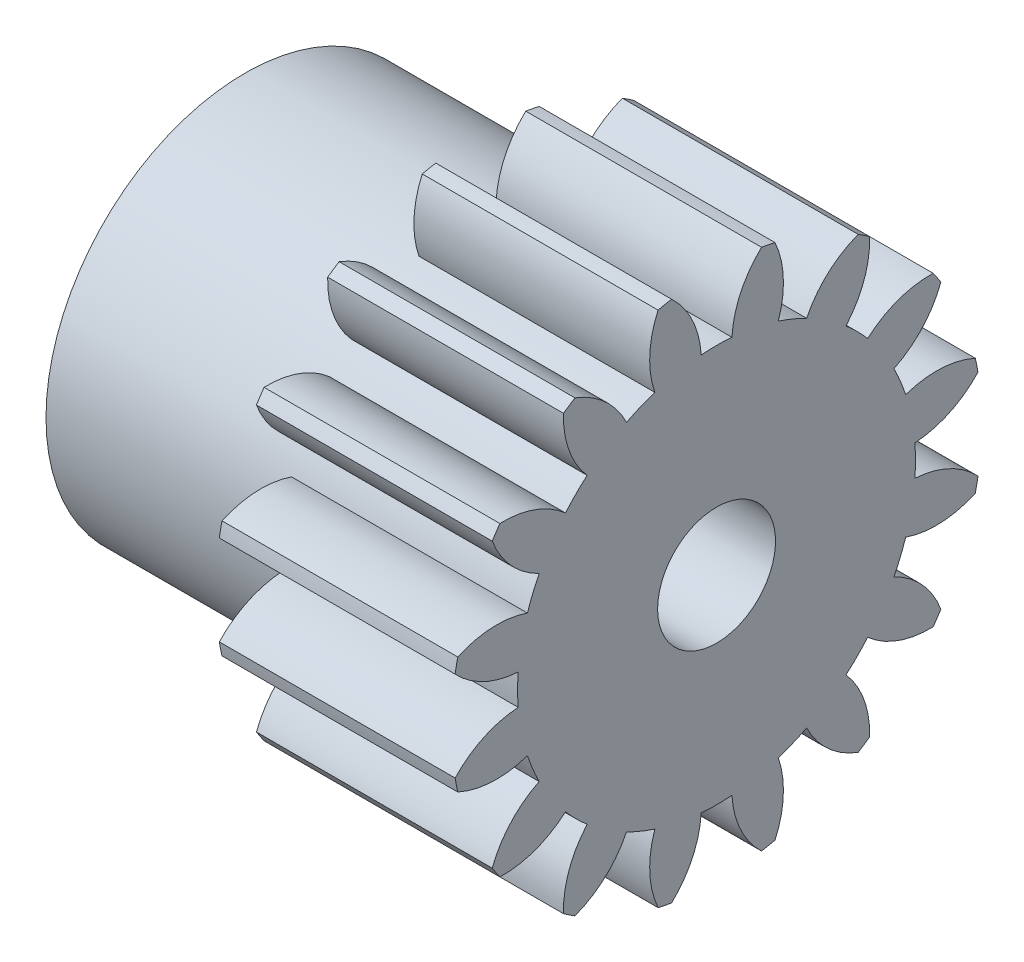
SolidWorks part; units mm, degrees
ref_plane "Plane1" through (0, 0, 0) normal (0, 0, 1) x (1, 0, 0)
ref_plane "Plane2" through (0, 0, 0) normal (0, 1, 0) x (1, 0, 0)
ref_plane "Plane3" through (0, 0, 0) normal (1, 0, 0) x (0, 0, -1)
sketch "HoldingSke" plane through (0, 0, 0) normal (0, 1, 0) x (1, 0, 0)
  line L0 (0, 0) -> (0.769, -0.2205)
  line L1 (-15, 0) -> (100, 0) construction
  line L2 (0, 0) -> (-2.1039, 2.3779)
  line L3 (0, 0) -> (-11.863, 4.5341)
  line L4 (0, 0) -> (8.3015, 2.3804)
  line L5 (0, 0) -> (-18.7391, -6.9891)
  line L6 (0, 0) -> (-8.2896, -5.593)
  line L7 (-2.1039, 2.3779) -> (2.2011, 21.9091)
  line L8 (-76.2, 54.61) -> (-75.3, 54.61)
  line L9 (-71.009, 38.7566) -> (-53.1078, 45.2721)
  line L10 (-76.2, 71.12) -> (104.1128, 71.12)
  line L11 (0, 0) -> (-10, 0)
  line L12 (-76.2, 101.6) -> (-76.155, 101.6)
  line L13 (24.9733, 27.94) -> (52.9518, 28.4284)
  line L14 (24.9733, 27.94) -> (24.9743, 27.94)
  line L15 (24.9733, 27.94) -> (100.4006, 29.5858)
  line L16 (-63.627, -1.25) -> (-12.827, -1.25)
  circle A0 centre (0, 0) radius 2.5
  circle A1 centre (0, 0) radius 8.4365
  circle A2 centre (0, 0) radius 20
  circle A3 centre (0, 0) radius 2.5
  dimension "MHD" = 16.873
  dimension "Hub_dia" = 40
  dimension "Bore" = 5
  dimension "MBD" = 5
  dimension "Num_teeth" = 16
  dimension "Pitch" = 0.8
  dimension "Overall_len" = 20
  dimension "Show_teeth" = 16
  dimension "Thickness" = 10
  dimension "OAL" = 20.0001
  dimension "T_dim" = 0.9
  dimension "Ap" = 20
  dimension "H" = 19.05
  dimension "Pitch_radius" = 180.3128
  dimension "Width" = 10
  dimension "Backlash" = 0.045
  dimension "Addendum_fac" = 1
  dimension "Dedendum_fac" = 1.25
  dimension "Clearance_fac" = 0.25
  dimension "Dedendum_add" = 0.001
  dimension "Module" = 1.25
sketch "BasProSke" plane through (0, 0, 0) normal (0, 1, 0) x (1, 0, 0)
  line L0 (-10, 0) -> (60, 0) construction
  line L1 (0, 0) -> (0, 11.25)
  line L2 (0, 0) -> (10, 0)
  line L3 (10, 0) -> (10, 11.25)
  line L4 (10, 11.25) -> (0, 11.25)
  dimension "Thickness" = 10
  dimension "Diameter" = 22.5
revolve "Base-Revolve" add sketch "BasProSke" angle 360 about L0
sketch "TooCutSke" plane through (0, 0, 0) normal (1, 0, 0) x (0, 0, -1)
  line L1 (0, 0) -> (0, 107) construction
  line L2 (0, 0) -> (-1.0589, 9.9438) construction
  line L3 (0, 0) -> (-3.8859, 19.5358) construction
  line L4 (-1.0589, 9.9438) -> (-1.943, 9.7679) construction
  arc A0 (0.6511, 8.4113) -> (-0.6511, 8.4113) centre (0, 0) ccw
  arc A1 (1.9309, 11.1088) -> (-1.9309, 11.1088) centre (0, 0) ccw
  circle A2 centre (0, 0) radius 10 construction
  circle A3 centre (0, 0) radius 9.3969 construction
  arc A4 (-0.6511, 8.4113) -> (-1.9309, 11.1088) centre (-4.6437, 8.1693) ccw
  arc A5 (1.9309, 11.1088) -> (0.6511, 8.4113) centre (4.6437, 8.1693) ccw
  dimension "Root_dia" = 16.873
  dimension "Overcut_dia" = 22.5508
  dimension "Pitch_dia" = 20
  dimension "Base_dia" = 18.7939
  dimension "Flank_rad" = 4
  dimension "Half_ang" = 11.25
  dimension "Half_CT" = 0.9014
extrude "ToothCut" cut sketch "TooCutSke" along normal through all
fillet "Breaks" [suppressed] radius 0.025
fillet "RootFillets" [suppressed] radius 0.3135
pattern_circular "TeethCuts" count 16 every 22.5 about axis through (-10, 0, 0) along (1, 0, 0) of "ToothCut", "RootFillets", "Breaks"
sketch "HubNeaOneSke" plane through (0, 0, 0) normal (-1, 0, 0) x (0, 0, 1)
  circle A0 centre (0, 0) radius 8.4365
  dimension "Diameter" = 16.873
extrude "HubNearOne" add sketch "HubNeaOneSke" along normal blind 10.0001
sketch "HubNeaBotSke" plane through (0, 0, 0) normal (-1, 0, 0) x (0, 0, 1)
  circle A0 centre (0, 0) radius 8.4365
  dimension "Diameter" = 16.873
extrude "HubNearBoth" [suppressed] add sketch "HubNeaBotSke" along normal blind 5
ref_plane "FarPln" through (10, 0, 0) normal (1, 0, 0) x (0, 0, -1)
sketch "HubFarSke" plane through (10, 0, 0) normal (1, 0, 0) x (0, 0, -1)
  circle A0 centre (0, 0) radius 8.4365
  dimension "Diameter" = 16.873
extrude "HubFar" [suppressed] add sketch "HubFarSke" along normal blind 5
sketch "BorSke" plane through (0, 0, 0) normal (1, 0, 0) x (0, 0, -1)
  circle A0 centre (0, 0) radius 2.5
  dimension "Diameter" = 5
extrude "Bore" cut sketch "BorSke" along normal mid plane 40.0001
sketch "KeySke" plane through (0, 0, 0) normal (1, 0, 0) x (0, 0, -1)
  line L0 (-1, 0) -> (-1, 3.4)
  line L1 (-1, 3.4) -> (1, 3.4)
  line L2 (1, 3.4) -> (1, 0)
  line L3 (0, 0) -> (0, 34) construction
  line L4 (-1, 0) -> (1, 0)
  dimension "Offset" = 3.4
  dimension "Width" = 2
extrude "Keyway" [suppressed] cut sketch "KeySke" along normal mid plane 40.0001
pattern_circular "Keyway2" [suppressed] count 2 every 90 about axis through (-10, 0, 0) along (1, 0, 0)
equation "' \"Module@HoldingSke\" = 6.35"
equation "' \"Num_teeth@HoldingSke\" = 12"
equation "' \"Ap@HoldingSke\" =  20"
equation "' \"Ap@HoldingSke\" = 20"
equation "' \"Width@HoldingSke\" = 0.5 * 25.4"
equation "' \"Hub_dia@HoldingSke\"= 1 * 25.4"
equation "' \"Hub_dia@HoldingSke\" = 1 * 25.4"
equation "' \"Overall_len@HoldingSke\" = 1.0 * 25.4"
equation "' \"Bore@HoldingSke\" = 0.75 * 25.4"
equation "' \"T_dim@HoldingSke\" = 0.1 * 25.4"
equation "' \"Width@KeySke\" = 0.25 * 25.4"
equation "' \"Show_teeth@HoldingSke\" = 13"
equation "' \"Backlash@HoldingSke\" = 0.009 * 25.4"
equation "' \"Addendum_fac@HoldingSke\" = 1.0"
equation "' \"Dedendum_fac@HoldingSke\" = 1.25"
equation "' \"Dedendum_add@HoldingSke\" = 0.00005 * 25.4"
equation "' \"Clearance_fac@HoldingSke\" = 0.25"
equation "\"Pitch@HoldingSke\" = 1 / \"Module@HoldingSke\""
equation "\"Overcut_dia@TooCutSke\" = (\"Num_teeth@HoldingSke\" + 2 * \"Addendum_fac@HoldingSke\") / \"Pitch@HoldingSke\" + 0.002 * 25.4"
equation "\"Pitch_dia@TooCutSke\" = \"Num_teeth@HoldingSke\" / \"Pitch@HoldingSke\""
equation "\"Base_dia@TooCutSke\" = \"Num_teeth@HoldingSke\" / \"Pitch@HoldingSke\" * cos((\"Ap@HoldingSke\"  * 3.14159265 / 180))"
equation "\"Root_dia@TooCutSke\" = (\"Num_teeth@HoldingSke\" + 2) / \"Pitch@HoldingSke\" - 2 * (\"Addendum_fac@HoldingSke\" + \"Dedendum_fac@HoldingSke\") / \"Pitch@HoldingSke\" - \"Dedendum_add@HoldingSke\" * 2"
equation "\"Half_ang@TooCutSke\" = 180 / \"Num_teeth@HoldingSke\""
equation "\"Half_CT@TooCutSke\" = \"Num_teeth@HoldingSke\" / \"Pitch@HoldingSke\" * sin((3.14159265 / 2 / \"Num_teeth@HoldingSke\")) / 2 - 7 * \"Backlash@HoldingSke\" / 4"
equation "\"Flank_rad@TooCutSke\" = \"Num_teeth@HoldingSke\" / \"Pitch@HoldingSke\" / 5"
equation "\"Radius@RootFillets\" = \"Clearance_fac@HoldingSke\" / \"Pitch@HoldingSke\" + \"Dedendum_add@HoldingSke\""
equation "\"Break_rad@Breaks\" = 0.02 / \"Pitch@HoldingSke\""
equation "\"Thickness@HoldingSke\" = \"Width@HoldingSke\""
equation "\"OAL@HoldingSke\" = \"Thickness@HoldingSke\""
equation "\"MHD@HoldingSke\" = (\"Num_teeth@HoldingSke\" + 2) / \"Pitch@HoldingSke\" - 2 * (\"Addendum_fac@HoldingSke\" + \"Dedendum_fac@HoldingSke\")  / \"Pitch@HoldingSke\" - \"Dedendum_add@HoldingSke\" * 2"
equation "\"MBD@HoldingSke\" = (\"Num_teeth@HoldingSke\" + 2) / \"Pitch@HoldingSke\" - 2 * (\"Addendum_fac@HoldingSke\" + \"Dedendum_fac@HoldingSke\")  / \"Pitch@HoldingSke\" - \"Dedendum_add@HoldingSke\" * 2 - 0.002 * 25.4"
equation "\"MHD@HoldingSke\" = ((sgn( \"MHD@HoldingSke\" - \"Hub_dia@HoldingSke\" )-1)*( \"MHD@HoldingSke\" - \"Hub_dia@HoldingSke\" ))/-2+ \"Hub_dia@HoldingSke\""
equation "\"MBD@HoldingSke\" = ((sgn( \"MBD@HoldingSke\" - \"Bore@HoldingSke\" )-1)*( \"MBD@HoldingSke\" - \"Bore@HoldingSke\" ))/-2+ \"Bore@HoldingSke\""
equation "\"OAL@HoldingSke\" = ((sgn( \"OAL@HoldingSke\" - \"Overall_len@HoldingSke\" )+1)*( \"OAL@HoldingSke\" - \"Overall_len@HoldingSke\" ))/2 + \"Overall_len@HoldingSke\" + 0.000002 * 25.4"
equation "\"Num_teeth@TeethCuts\" = int( \"Show_teeth@HoldingSke\" ) + 1"
equation "\"Num_teeth@TeethCuts\" = ((sgn( \"Num_teeth@TeethCuts\" - \"Num_teeth@HoldingSke\" )-1)*( \"Num_teeth@TeethCuts\" - \"Num_teeth@HoldingSke\" ))/-2+ \"Num_teeth@HoldingSke\""
equation "\"Num_teeth@TeethCuts\" = ((sgn( \"Num_teeth@TeethCuts\" - 2.0)+1)*( \"Num_teeth@TeethCuts\" - 2.0))/2 +2.0"
equation "\"Angle@TeethCuts\" = 360.0 / \"Num_teeth@HoldingSke\""
equation "\"Diameter@BasProSke\" = (\"Num_teeth@HoldingSke\" + 2 * \"Addendum_fac@HoldingSke\") / \"Pitch@HoldingSke\""
equation "\"Thickness@BasProSke\"  = \"Thickness@HoldingSke\""
equation "' \"Fillet_rad@BasProSke\" =  \"Thickness@HoldingSke\" * 0.05"
equation "' \"Fillet_rad@BasProSke\" = \"Thickness@HoldingSke\" * 0.05"
equation "\"MHD@HoldingSke\" = ((sgn( \"MHD@HoldingSke\" - \"Root_dia@TooCutSke\" )-1)*( \"MHD@HoldingSke\" - \"Root_dia@TooCutSke\" ))/-2+ \"Root_dia@TooCutSke\""
equation "\"Diameter@HubNeaOneSke\" = \"MHD@HoldingSke\""
equation "\"Length@HubNearOne\" = \"OAL@HoldingSke\" - \"Thickness@BasProSke\""
equation "\"Diameter@HubNeaBotSke\" = \"MHD@HoldingSke\""
equation "\"Length@HubNearBoth\" = ( \"OAL@HoldingSke\" - \"Thickness@BasProSke\" ) / 2.0"
equation "\"Thickness@FarPln\" = \"Thickness@BasProSke\""
equation "\"Diameter@HubFarSke\" = \"MHD@HoldingSke\""
equation "\"Length@HubFar\" = ( \"OAL@HoldingSke\" - \"Thickness@BasProSke\" ) / 2.0"
equation "\"Diameter@BorSke\" = \"MBD@HoldingSke\""
equation "\"D1@Bore\" = \"OAL@HoldingSke\" * 2.0"
equation "\"D1@Keyway\" = \"OAL@HoldingSke\" * 2.0"
equation "\"Offset@KeySke\" = \"T_dim@HoldingSke\" + \"MBD@HoldingSke\" / 2.0"
